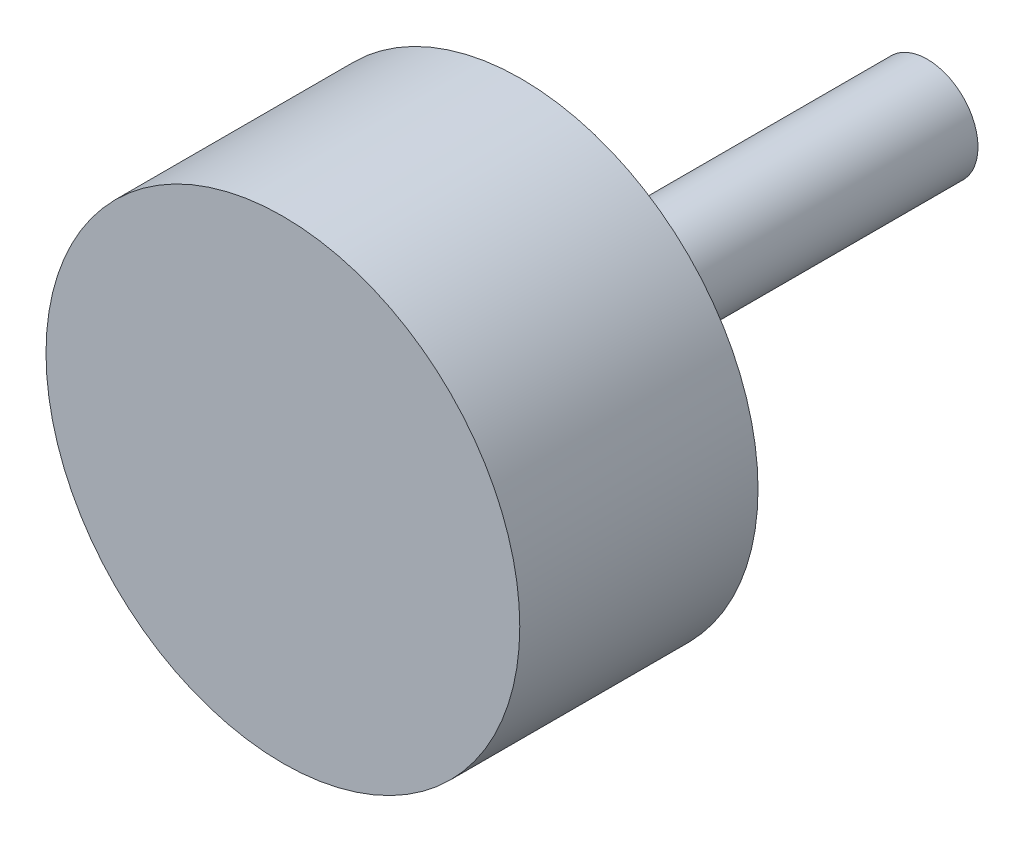
SolidWorks part; units mm, degrees
ref_plane "Front Plane" through (0, 0, 0) normal (0, 0, 1) x (1, 0, 0)
ref_plane "Top Plane" through (0, 0, 0) normal (0, 1, 0) x (1, 0, 0)
ref_plane "Right Plane" through (0, 0, 0) normal (1, 0, 0) x (0, 0, -1)
sketch "Sketch1" plane through (0, 0, 0) normal (0, 0, 1) x (1, 0, 0)
  circle A0 centre (0, 0) radius 22.225
  dimension "D1" = 44.45
extrude "Boss-Extrude1" add sketch "Sketch1" along normal blind 22.352
sketch "Sketch2" plane through (0, 0, 0) normal (0, 0, 1) x (1, 0, 0)
  circle A0 centre (0, 0) radius 4.7625
  dimension "D1" = 9.525
extrude "Boss-Extrude2" add sketch "Sketch2" against normal blind 38.1
